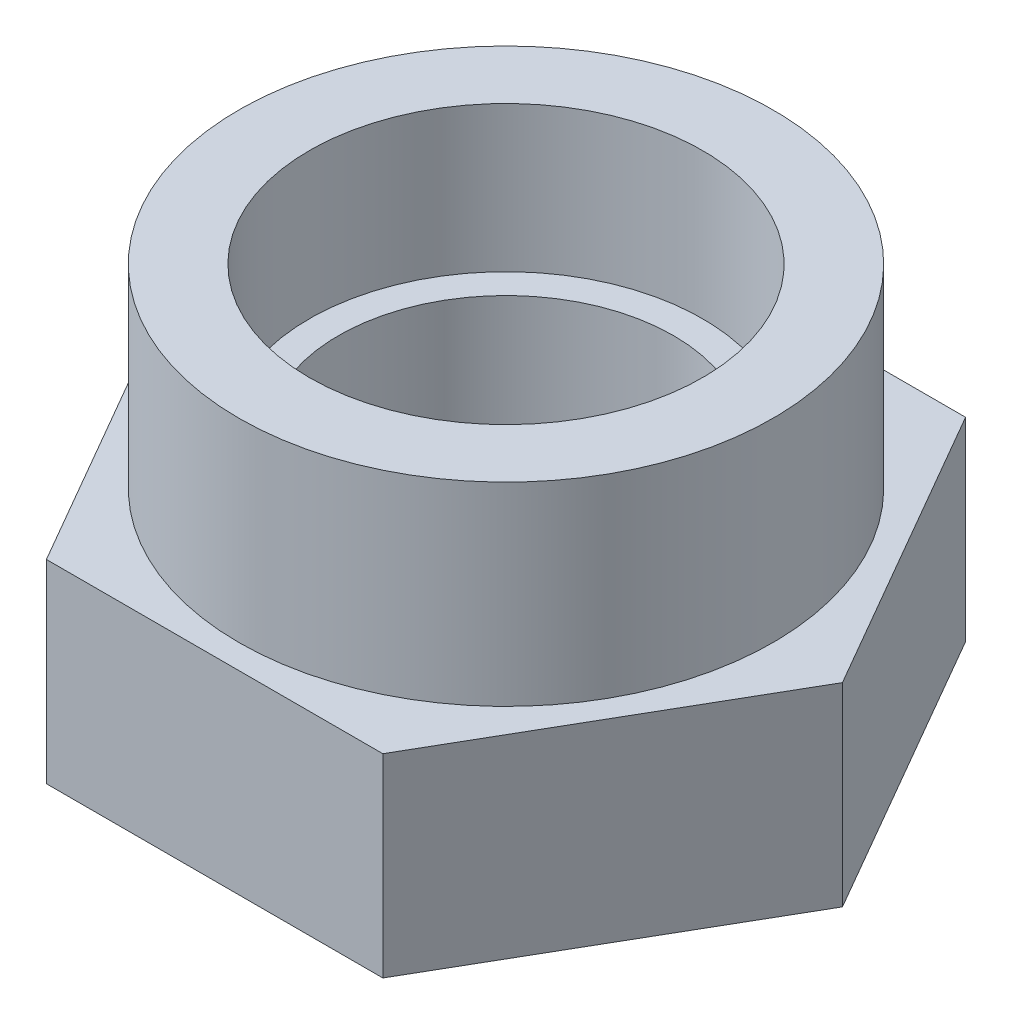
SolidWorks part; units mm, degrees
ref_plane "Front Plane" through (0, 0, 0) normal (0, 0, 1) x (1, 0, 0)
ref_plane "Top Plane" through (0, 0, 0) normal (0, 1, 0) x (1, 0, 0)
ref_plane "Right Plane" through (0, 0, 0) normal (1, 0, 0) x (0, 0, -1)
sketch "Sketch1" plane through (0, 0, 0) normal (0, 1, 0) x (1, 0, 0)
  line L1 (3.4641, 6) -> (-3.4641, 6)
  line L2 (-3.4641, 6) -> (-6.9282, 0)
  line L3 (-6.9282, 0) -> (-3.4641, -6)
  line L4 (-3.4641, -6) -> (3.4641, -6)
  line L5 (3.4641, -6) -> (6.9282, 0)
  line L6 (6.9282, 0) -> (3.4641, 6)
  circle A0 centre (0, 0) radius 6 construction
  circle A1 centre (0, 0) radius 3.45
  dimension "D2" = 6.9
  dimension "D1" = 12
extrude "Boss-Extrude1" add sketch "Sketch1" along normal blind 8
sketch "Sketch2" plane through (0, 8, 0) normal (0, 1, 0) x (1, 0, 0)
  circle A0 centre (0, 0) radius 4.05
  dimension "D1" = 8.1
extrude "Cut-Extrude1" cut sketch "Sketch2" against normal blind 3
sketch "Sketch3" plane through (0, 8, 0) normal (0, 1, 0) x (1, 0, 0)
  circle A0 centre (0, 0) radius 5.5
  circle A1 centre (0, 0) radius 10
  line M4 (6.9282, 0) -> (3.4641, 6)
  line M5 (3.4641, 6) -> (-3.4641, 6)
  line M6 (-3.4641, 6) -> (-6.9282, 0)
  line M7 (-6.9282, 0) -> (-3.4641, -6)
  line M8 (-3.4641, -6) -> (3.4641, -6)
  line M9 (3.4641, -6) -> (6.9282, 0)
  dimension "D1" = 20
  dimension "D2" = 11
extrude "Cut-Extrude3" cut sketch "Sketch3" against normal blind 4 contours A1 M4 M9 M8 M7 M6 M5 | A0 M9 M4 M5 M6 M7 M8
